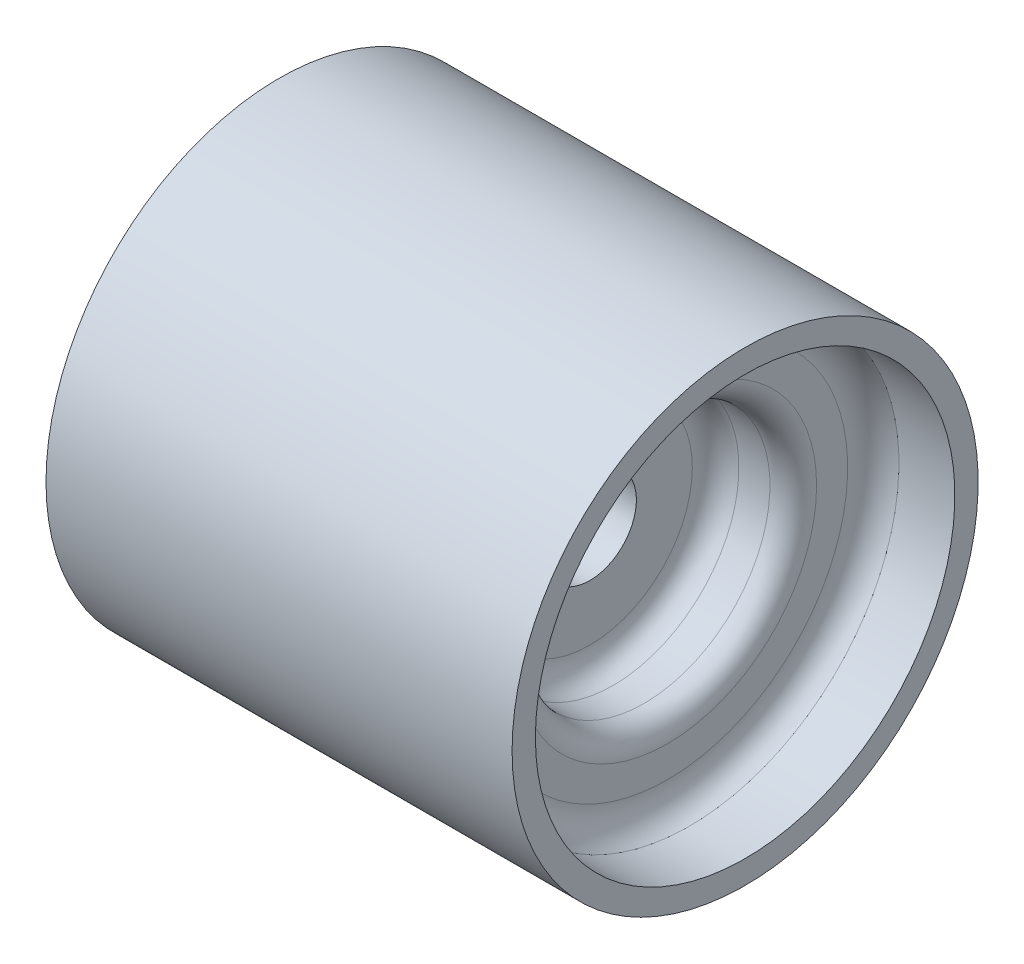
SolidWorks part; units mm, degrees
ref_plane "Front Plane" through (0, 0, 0) normal (0, 0, 1) x (1, 0, 0)
ref_plane "Top Plane" through (0, 0, 0) normal (0, 1, 0) x (1, 0, 0)
ref_plane "Right Plane" through (0, 0, 0) normal (1, 0, 0) x (0, 0, -1)
sketch "Sketch1" plane through (0, 0, 0) normal (0, 0, 1) x (1, 0, 0)
  line L8 (-42.3333, 63.5) -> (84.6667, 63.5)
  line L15 (42.3333, 12.7) -> (0, 12.7)
  line L17 (0, 0) -> (112.9708, 0) construction
  line L18 (42.3333, 12.7) -> (42.3333, 27.94)
  line L21 (69.4267, 57.15) -> (84.6667, 57.15)
  line L22 (84.6667, 57.15) -> (84.6667, 63.5)
  line L23 (0, 12.7) -> (0, 27.8553)
  line L24 (63.5, 49.1067) -> (63.5, 40.64)
  line L25 (48.6833, 34.29) -> (57.15, 34.29)
  line L26 (-6.35, 34.2053) -> (-14.732, 34.2053)
  line L27 (-21.082, 40.5553) -> (-21.082, 49.022)
  line L28 (-27.0933, 57.15) -> (-42.3333, 57.15)
  line L29 (-42.3333, 57.15) -> (-42.3333, 63.5)
  arc A18 (63.5, 49.1067) -> (69.4267, 57.15) centre (71.0957, 49.715) cw
  arc A19 (63.5, 40.64) -> (57.15, 34.29) centre (57.15, 40.64) cw
  arc A20 (48.6833, 34.29) -> (42.3333, 27.94) centre (48.6833, 27.94) ccw
  arc A21 (0, 27.8553) -> (-6.35, 34.2053) centre (-6.35, 27.8553) ccw
  arc A22 (-14.732, 34.2053) -> (-21.082, 40.5553) centre (-14.478, 40.8093) cw
  arc A23 (-21.082, 49.022) -> (-27.0933, 57.15) centre (-28.6722, 49.6954) ccw
  dimension "D3" = 7.62
  dimension "D6" = 6.35
  dimension "D8" = 8.4667
  dimension "D11" = 42.3333
  dimension "D13" = 6.35
  dimension "D14" = 7.62
  dimension "D17" = 50.8
  dimension "D15" = 127
  dimension "D25" = 8.4667
  dimension "D29" = 8.128
  dimension "D2" = 6.35
  dimension "D7" = 8.4667
  dimension "D5" = 6.35
  dimension "D28" = 8.128
  dimension "D4" = 12.7
  dimension "D9" = 15.24
  dimension "D10" = 15.24
  dimension "D12" = 6.35
  dimension "D16" = 6.35
  dimension "D18" = 42.3333
  dimension "D19" = 6.35
  dimension "D20" = 6.35
  dimension "D21" = 6.35
  dimension "D22" = 8.382
  dimension "D23" = 6.35
  dimension "D24" = 6.35
  dimension "D26" = 15.24
  dimension "D27" = 6.35
revolve "Revolve1" add sketch "Sketch1" angle 360 about L17
